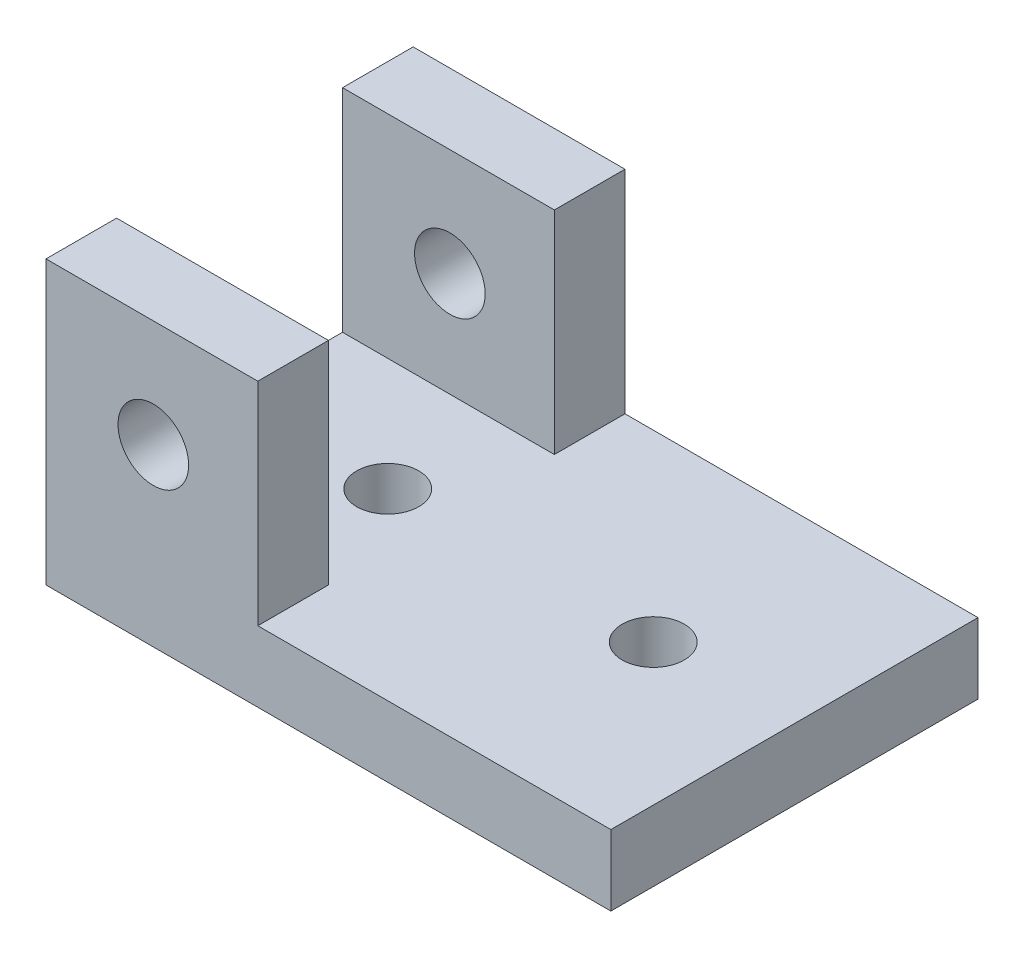
SolidWorks part; units mm, degrees
ref_plane "Front Plane" through (0, 0, 0) normal (0, 0, 1) x (1, 0, 0)
ref_plane "Top Plane" through (0, 0, 0) normal (0, 1, 0) x (1, 0, 0)
ref_plane "Right Plane" through (0, 0, 0) normal (1, 0, 0) x (0, 0, -1)
sketch "Sketch3" plane through (0, 0, 0) normal (0, 1, 0) x (1, 0, 0)
  line L0 (0, 0) -> (0, 33.02)
  line L1 (0, -55) -> (0, 55) construction
  line L2 (0, 33.02) -> (50.8, 33.02)
  line L3 (50.8, 33.02) -> (50.8, 0)
  line L4 (-55, 0) -> (55, 0) construction
  line L5 (50.8, 0) -> (0, 0)
extrude "Boss-Extrude2" add sketch "Sketch3" along normal blind 6.35
sketch "Sketch4" plane through (0, 6.35, 0) normal (0, 1, 0) x (1, 0, 0)
  circle A0 centre (14.224, 16.51) radius 2.794
  circle A1 centre (38.1, 16.51) radius 2.794
extrude "Cut-Extrude1" cut sketch "Sketch4" against normal through all
sketch "Sketch5" plane through (0, 6.35, 0) normal (0, 1, 0) x (1, 0, 0)
  line L0 (0, 0) -> (19.05, 0)
  line L1 (19.05, 0) -> (19.05, 6.35)
  line L2 (19.05, 6.35) -> (0, 6.35)
  line L3 (0, 6.35) -> (0, 0)
extrude "Boss-Extrude3" add sketch "Sketch5" along normal blind 19.05
sketch "Sketch6" plane through (0, 6.35, 0) normal (0, 1, 0) x (1, 0, 0)
  line L0 (14.224, 16.51) -> (0, 16.51)
  line L1 (0, 33.02) -> (0, 6.35) construction
ref_plane "Plane1" through (0, 0, -16.51) normal (0, 0, 1) x (1, 0, 0)
mirror "Mirror1" about plane through (0, 0, -16.51) normal (0, 0, 1) of "Boss-Extrude3"
sketch "Sketch7" plane through (0, 0, 0) normal (0, 0, 1) x (1, 0, 0)
  circle A0 centre (9.652, 15.748) radius 3.175
extrude "Cut-Extrude2" cut sketch "Sketch7" against normal blind 34.29
